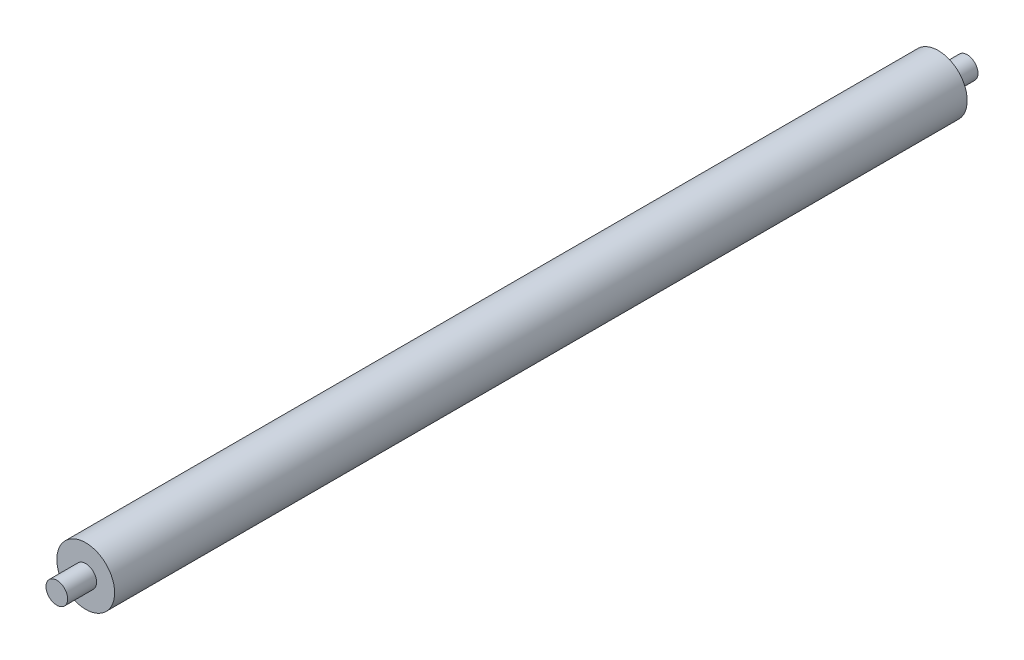
SolidWorks part; units mm, degrees
ref_plane "前视基准面" through (0, 0, 0) normal (0, 0, 1) x (1, 0, 0)
ref_plane "上视基准面" through (0, 0, 0) normal (0, 1, 0) x (1, 0, 0)
ref_plane "右视基准面" through (0, 0, 0) normal (1, 0, 0) x (0, 0, -1)
sketch "草图1" plane through (0, 0, 0) normal (0, 0, 1) x (1, 0, 0)
  circle A0 centre (0, 0) radius 4
extrude "凸台-拉伸1" add sketch "草图1" along normal blind 118
sketch "草图2" plane through (0, 0, 0) normal (0, 0, -1) x (-1, 0, 0)
  circle A0 centre (0, 0) radius 1.5
extrude "凸台-拉伸2" add sketch "草图2" along normal blind 4
sketch "草图3" plane through (0, 0, 118) normal (0, 0, 1) x (1, 0, 0)
  circle A0 centre (0, 0) radius 1.5
extrude "凸台-拉伸3" add sketch "草图3" along normal blind 4
